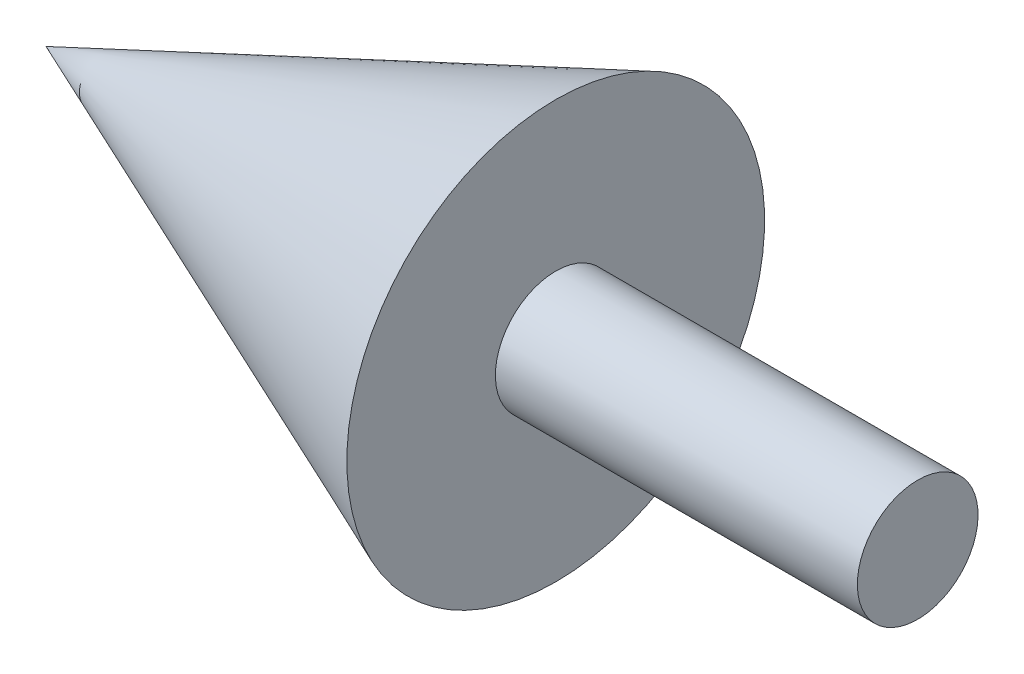
SolidWorks part; units mm, degrees
material "1060 Legierung"
ref_plane "Ebene vorne" through (0, 0, 0) normal (0, 0, 1) x (1, 0, 0)
ref_plane "Ebene oben" through (0, 0, 0) normal (0, 1, 0) x (1, 0, 0)
ref_plane "Ebene rechts" through (0, 0, 0) normal (1, 0, 0) x (0, 0, -1)
sketch "Skizze2" plane through (0, 0, 0) normal (0, 0, 1) x (1, 0, 0)
  line L0 (0, 0) -> (299.9061, 0)
  line L1 (299.9061, 0) -> (299.9061, 61.5) construction
  line L2 (299.9061, 0) -> (329.9061, 0)
  line L3 (329.9061, 0) -> (329.9061, 61.5)
  line L4 (329.9061, 61.5) -> (299.9061, 61.5)
  spline S0 degree 4 poles (0, 0) (0.0016, 0.0111) (0.006, 0.0331) (0.0193, 0.076) (0.0528, 0.1594) (0.0995, 0.2524) (0.1584, 0.3549) (0.2445, 0.4907) (0.3798, 0.6852) (0.6296, 1.0032) (1.0945, 1.5185) (1.9101, 2.3025) (3.3122, 3.4727) (5.686, 5.1914) (9.584, 7.6386) (15.5853, 10.9037) (24.4163, 15.0805) (37.3073, 20.3717) (53.7306, 26.1534) (73.0107, 31.9777) (94.1601, 37.4597) (112.8151, 41.633) (128.8872, 44.8146) (142.3261, 47.2203) (153.1016, 49.0037) (163.8986, 50.6515) (174.7148, 52.1685) (185.5479, 53.5593) (196.3961, 54.8279) (207.257, 55.9783) (216.7711, 56.8847) (224.9312, 57.5924) (233.0976, 58.246) (241.2647, 58.8463) (249.4427, 59.3822) (257.6143, 59.8555) (264.4402, 60.2101) (269.8782, 60.4696) (275.3665, 60.7072) (280.0845, 60.8934) (284.2679, 61.0427) (287.5343, 61.153) (290.5234, 61.245) (293.4329, 61.3336) (297.9807, 61.454) (300.9026, 61.5257) (305.7428, 61.6322) (309.1565, 61.6967) (313.105, 61.7657) (316.7318, 61.8189) (320.5634, 61.8694) (324.2516, 61.9091) (327.1123, 61.936) (328.9581, 61.9504) (329.9077, 61.9576) knots 0 0 0 0 0 0.000132 0.000264 0.000528 0.001056 0.001356 0.001655 0.002421 0.003844 0.006112 0.009819 0.015728 0.025326 0.040588 0.063964 0.096107 0.140272 0.204558 0.268843 0.333129 0.397415 0.429558 0.4617 0.493843 0.525986 0.558129 0.590272 0.622415 0.654558 0.6867 0.702772 0.718843 0.750986 0.783129 0.7992 0.815272 0.831343 0.847415 0.863486 0.871522 0.879558 0.887593 0.895629 0.9117 0.922738 0.933775 0.944813 0.95585 0.966888 0.977925 0.988963 1 1 1 1 1 construction
  spline S1 degree 4 poles (0, 0) (0.0016, 0.0111) (0.006, 0.0331) (0.0193, 0.076) (0.0528, 0.1594) (0.0995, 0.2524) (0.1584, 0.3549) (0.2445, 0.4907) (0.3798, 0.6852) (0.6296, 1.0032) (1.0945, 1.5185) (1.9101, 2.3025) (3.3122, 3.4727) (5.686, 5.1914) (9.584, 7.6386) (15.5853, 10.9037) (24.4163, 15.0805) (37.3073, 20.3717) (53.7306, 26.1534) (73.0107, 31.9777) (94.1601, 37.4597) (112.8151, 41.633) (128.8872, 44.8146) (142.3261, 47.2203) (153.1016, 49.0037) (163.8986, 50.6515) (174.7148, 52.1685) (185.5479, 53.5593) (196.3961, 54.8279) (207.257, 55.9783) (216.7711, 56.8847) (224.9312, 57.5924) (233.0976, 58.246) (241.2647, 58.8463) (249.4427, 59.3822) (257.6143, 59.8555) (264.4402, 60.2101) (269.8782, 60.4696) (275.3665, 60.7072) (280.0845, 60.8934) (284.2679, 61.0427) (287.5343, 61.153) (290.5234, 61.245) (293.4329, 61.3336) (296.8182, 61.4233) (298.6618, 61.4701) (299.9061, 61.5) knots 0 0 0 0 0 0.000132 0.000264 0.000528 0.001056 0.001356 0.001655 0.002421 0.003844 0.006112 0.009819 0.015728 0.025326 0.040588 0.063964 0.096107 0.140272 0.204558 0.268843 0.333129 0.397415 0.429558 0.4617 0.493843 0.525986 0.558129 0.590272 0.622415 0.654558 0.6867 0.702772 0.718843 0.750986 0.783129 0.7992 0.815272 0.831343 0.847415 0.863486 0.871522 0.879558 0.887593 0.895629 0.9117 0.9117 0.9117 0.9117 0.9117
  dimension "D1" = 61.5
  dimension "D2" = 30
ref_plane "Ebene3" through (15, 0, 0) normal (1, 0, 0) x (0, 0, -1)
sketch "Skizze8" plane through (0, 0, 0) normal (0, 0, 1) x (1, 0, 0)
  line L0 (-12.2459, 0) -> (30, 17.3133)
  line L2 (30, 5) -> (30, 17.3133)
  line L3 (30, 5) -> (60, 5)
  line L4 (60, 5) -> (60, 0)
  line L5 (60, 0) -> (-12.2459, 0)
  spline S0 degree 4 poles (0, 0) (0.0016, 0.0111) (0.006, 0.0331) (0.0193, 0.076) (0.0528, 0.1594) (0.0995, 0.2524) (0.1584, 0.3549) (0.2445, 0.4907) (0.3798, 0.6852) (0.6296, 1.0032) (1.0945, 1.5185) (1.9101, 2.3025) (3.3122, 3.4727) (5.686, 5.1914) (9.584, 7.6386) (15.5853, 10.9037) (24.4163, 15.0805) (37.3073, 20.3717) (53.7306, 26.1534) (73.0107, 31.9777) (94.1601, 37.4597) (112.8151, 41.633) (128.8872, 44.8146) (142.3261, 47.2203) (153.1016, 49.0037) (163.8986, 50.6515) (174.7148, 52.1685) (185.5479, 53.5593) (196.3961, 54.8279) (207.257, 55.9783) (216.7711, 56.8847) (224.9312, 57.5924) (233.0976, 58.246) (241.2647, 58.8463) (249.4427, 59.3822) (257.6143, 59.8555) (264.4402, 60.2101) (269.8782, 60.4696) (275.3665, 60.7072) (280.0845, 60.8934) (284.2679, 61.0427) (287.5343, 61.153) (290.5234, 61.245) (293.4329, 61.3336) (296.8182, 61.4233) (298.6618, 61.4701) (299.9061, 61.5) knots 0 0 0 0 0 0.000132 0.000264 0.000528 0.001056 0.001356 0.001655 0.002421 0.003844 0.006112 0.009819 0.015728 0.025326 0.040588 0.063964 0.096107 0.140272 0.204558 0.268843 0.333129 0.397415 0.429558 0.4617 0.493843 0.525986 0.558129 0.590272 0.622415 0.654558 0.6867 0.702772 0.718843 0.750986 0.783129 0.7992 0.815272 0.831343 0.847415 0.863486 0.871522 0.879558 0.887593 0.895629 0.9117 0.9117 0.9117 0.9117 0.9117 construction
  dimension "D1" = 30
  dimension "D2" = 30
  dimension "D3" = 5
revolve "Rotation3" add sketch "Skizze8" angle 360 about L5
equation "\"L\"= 350'length"
equation "\"C\"= 2 / 3'C-value"
